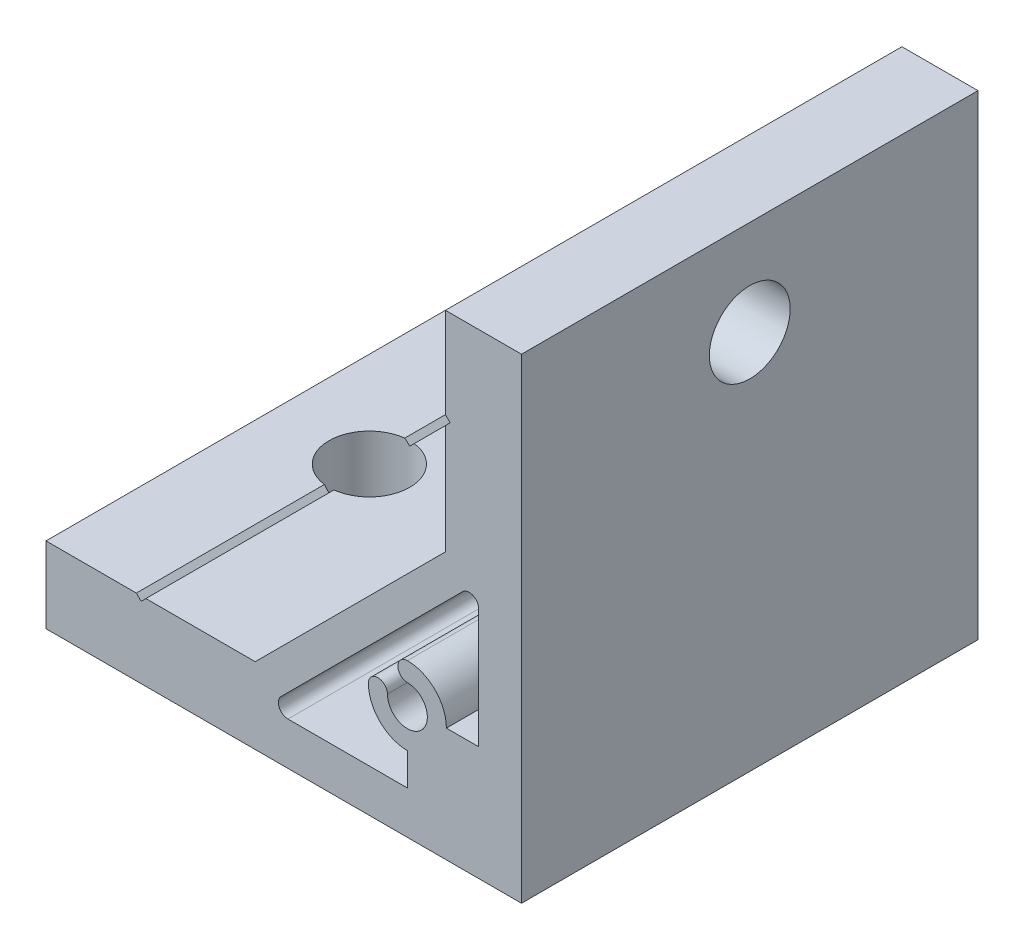
SolidWorks part; units mm, degrees
material "6063 T5"
ref_plane "Спереди" through (0, 0, 0) normal (0, 0, 1) x (1, 0, 0)
ref_plane "Сверху" through (0, 0, 0) normal (0, 1, 0) x (1, 0, 0)
ref_plane "Справа" through (0, 0, 0) normal (1, 0, 0) x (0, 0, -1)
sketch "Эскиз1" plane through (0, 0, 0) normal (0, 0, 1) x (1, 0, 0)
  line L0 (-50, 0) -> (0, 0)
  line L1 (0, 0) -> (0, 50)
  line L2 (0, 50) -> (-8, 50)
  line L3 (-8, 50) -> (-8, 40.5)
  line L4 (-8, 40.5) -> (-7.5, 40)
  line L5 (-7.5, 40) -> (-8, 39.5)
  line L6 (-8, 39.5) -> (-8, 28)
  line L7 (-8, 28) -> (-28, 8)
  line L8 (-28, 8) -> (-39.5, 8)
  line L9 (-39.5, 8) -> (-40, 7.5)
  line L10 (-40, 7.5) -> (-40.5, 8)
  line L11 (-40.5, 8) -> (-50, 8)
  line L12 (-50, 8) -> (-50, 0)
  line L13 (-4.5, 12) -> (-4.5, 24.5603)
  line L14 (-6.2071, 25.2674) -> (-25.2674, 6.2071)
  line L15 (-24.5603, 4.5) -> (-12, 4.5)
  line L16 (-12, 4.5) -> (-12, 7.9)
  line L17 (-7.9, 12) -> (-4.5, 12)
  arc A0 (-4.5, 24.5603) -> (-6.2071, 25.2674) centre (-5.5, 24.5603) ccw
  arc A1 (-25.2674, 6.2071) -> (-24.5603, 4.5) centre (-24.5603, 5.5) ccw
  arc A2 (-12, 7.9) -> (-16.1, 12) centre (-12, 12) cw
  arc A3 (-16.1, 12) -> (-14.1, 12) centre (-15.1, 12) cw
  arc A4 (-14.1, 12) -> (-12, 14.1) centre (-12, 12) ccw
  arc A5 (-12, 14.1) -> (-12, 16.1) centre (-12, 15.1) cw
  arc A6 (-12, 16.1) -> (-7.9, 12) centre (-12, 12) cw
  dimension "D6" = 4.2
  dimension "D7" = 1
  dimension "D9" = 1
  dimension "D1" = 50
  dimension "D2" = 8
  dimension "D3" = 135
  dimension "D4" = 12
  dimension "D5" = 12
  dimension "D8" = 28
  dimension "D10" = 3.2
  dimension "D11" = 4.5
  dimension "D12" = 40
  dimension "D13" = 1
extrude "Бобышка-Вытянуть1" add sketch "Эскиз1" along normal mid plane 48
sketch "Эскиз2" plane through (-8, 0, 0) normal (-1, 0, 0) x (0, 0, 1)
  line L0 (24, 40) -> (-24, 40) construction
  circle A0 centre (0, 40) radius 4.25
  dimension "D1" = 8.5
extrude "Вырез-Вытянуть1" cut sketch "Эскиз2" against normal through all
sketch "Эскиз3" plane through (0, 8, 0) normal (0, 1, 0) x (1, 0, 0)
  line L0 (-40, -24) -> (-40, 24) construction
  circle A0 centre (-40, 0) radius 4.25
  dimension "D1" = 8.5
extrude "Вырез-Вытянуть2" cut sketch "Эскиз3" against normal through all
